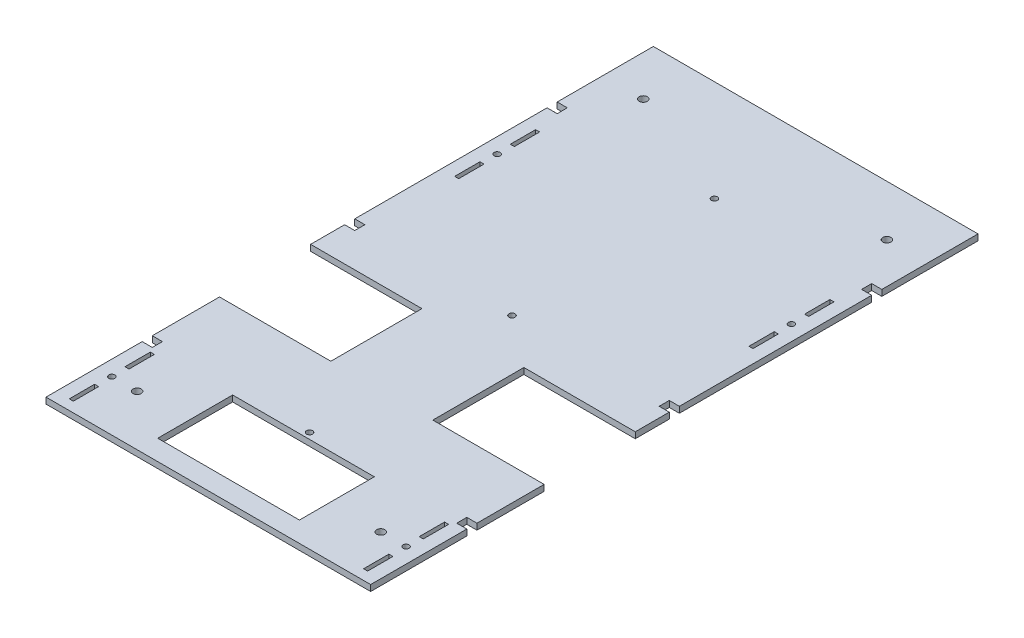
SolidWorks part; units mm, degrees
material "PMMA"
ref_plane "Front Plane" through (0, 0, 0) normal (0, 0, 1) x (1, 0, 0)
ref_plane "Top Plane" through (0, 0, 0) normal (0, 1, 0) x (1, 0, 0)
ref_plane "Right Plane" through (0, 0, 0) normal (1, 0, 0) x (0, 0, -1)
sketch "Schizzo1" plane through (0, 0, 0) normal (0, 1, 0) x (1, 0, 0)
  line L0 (-80.18, 150) -> (80.18, -150) construction
  line L1 (-80.18, 150) -> (80.18, 150)
  line L2 (-80.18, 150) -> (-80.18, -150)
  line L3 (-80.18, -150) -> (80.18, -150)
  line L4 (80.18, 150) -> (80.18, -150)
  point P4 (0, 0)
  dimension "D1" = 300
  dimension "D2" = 160.36
extrude "Estrusione-Estrusione1" add sketch "Schizzo1" along normal blind 3
sketch "Schizzo3" plane through (0, 0, 0) normal (0, 1, 0) x (1, 0, 0)
  line L0 (-80.18, 0) -> (80.18, 0) construction
  line L1 (-80.18, 150) -> (-80.18, -150) construction
  line L2 (0, 0) -> (0, -100) construction
  line L3 (0, 150) -> (0, -150) construction
  line L4 (80.18, 150) -> (-80.18, 150) construction
  line L5 (-80.18, -150) -> (80.18, -150) construction
  line L6 (0, 0) -> (0, 100) construction
  line L7 (-75.18, -97.5) -> (-80.18, -97.5)
  line L8 (-75.18, -2.5) -> (-80.18, -2.5)
  line L9 (-75.18, -2.5) -> (-75.18, 2.5)
  line L10 (-75.18, 2.5) -> (-80.18, 2.5)
  line L11 (-80.18, -2.5) -> (-80.18, 2.5)
  line L12 (-80.18, -102.5) -> (-80.18, -97.5)
  line L13 (-75.18, -102.5) -> (-80.18, -102.5)
  line L14 (-75.18, -102.5) -> (-75.18, -97.5)
  line L15 (-75.18, 2.5) -> (-75.18, -97.5) construction
  line L16 (-75.18, 97.5) -> (-80.18, 97.5)
  line L17 (-80.18, 97.5) -> (-80.18, 102.5)
  line L18 (-75.18, 102.5) -> (-80.18, 102.5)
  line L19 (-75.18, 97.5) -> (-75.18, 102.5)
  line L20 (-75.18, -2.5) -> (-75.18, 97.5) construction
  line L21 (75.18, -102.5) -> (75.18, -97.5)
  line L22 (75.18, -97.5) -> (80.18, -97.5)
  line L23 (80.18, -102.5) -> (80.18, -97.5)
  line L24 (75.18, -102.5) -> (80.18, -102.5)
  line L25 (75.18, -2.5) -> (75.18, 2.5)
  line L26 (75.18, 2.5) -> (80.18, 2.5)
  line L27 (80.18, -2.5) -> (80.18, 2.5)
  line L28 (75.18, -2.5) -> (80.18, -2.5)
  line L29 (75.18, 97.5) -> (75.18, 102.5)
  line L30 (75.18, 102.5) -> (80.18, 102.5)
  line L31 (80.18, 97.5) -> (80.18, 102.5)
  line L32 (75.18, 97.5) -> (80.18, 97.5)
  line L33 (-80.18, 150) -> (-80.18, -150) construction
  line L34 (-80.18, -19.3) -> (-25.18, -19.3)
  line L35 (-80.18, -19.3) -> (-80.18, -64.3)
  line L36 (-80.18, -64.3) -> (-25.18, -64.3)
  line L37 (-25.18, -19.3) -> (-25.18, -64.3)
  line L38 (80.18, -19.3) -> (80.18, -64.3)
  line L39 (80.18, -64.3) -> (25.18, -64.3)
  line L40 (25.18, -19.3) -> (25.18, -64.3)
  line L41 (80.18, -19.3) -> (25.18, -19.3)
  line L54 (80.18, -150) -> (80.18, 150) construction
  circle A0 centre (0, 0) radius 1.5
  circle A1 centre (0, -100) radius 1.5
  circle A2 centre (0, 100) radius 1.5
  circle A8 centre (-5.0427, -204.0432) radius 1.5
  point P24 (-80.18, 0)
  dimension "D1" = 3
  dimension "D2" = 100
  dimension "D4" = 100
  dimension "D5" = 5
  dimension "D6" = 5
  dimension "D7" = 100
  dimension "D9" = 100
  dimension "D11" = 55
  dimension "D12" = 45
  dimension "D13" = 16.8
  dimension "D3" = 2
  dimension "D8" = 2
  dimension "D10" = 2
extrude "Taglio-Estrusione1" cut sketch "Schizzo3" along direction (0, 1, 0) on the side of the normal through all
sketch "Schizzo4" plane through (0, 0, 0) normal (0, 1, 0) x (1, 0, 0)
  line L0 (-80.18, -102.5) -> (-80.18, -150) construction
  line L1 (-80.18, -150) -> (80.18, -150) construction
  line L2 (0, -150) -> (0, 150) construction
  line L3 (80.18, 150) -> (-80.18, 150) construction
  line L4 (75.18, 0) -> (-75.18, 0) construction
  line L5 (75.18, 2.5) -> (75.18, -2.5) construction
  line L6 (-75.18, -2.5) -> (-75.18, 2.5) construction
  circle A0 centre (-60.18, -125) radius 2
  circle A1 centre (60.18, -125) radius 2
  circle A2 centre (-60.18, 125) radius 2
  circle A3 centre (60.18, 125) radius 2
  dimension "D1" = 4
  dimension "D2" = 20
  dimension "D3" = 25
  dimension "D4" = 250
  dimension "D5" = 120.36
extrude "Taglio-Estrusione2" cut sketch "Schizzo4" along direction (0, 1, 0) on the side of the normal through all
sketch "Schizzo5" plane through (0, 0, 0) normal (0, 1, 0) x (1, 0, 0)
  line L0 (0, -150) -> (0, 150) construction
  line L1 (-80.18, -150) -> (80.18, -150) construction
  line L2 (80.18, 150) -> (-80.18, 150) construction
  line L3 (-80.18, -125) -> (80.18, -125) construction
  line L5 (80.18, -150) -> (80.18, -102.5) construction
  line L6 (-80.18, 65.35) -> (80.18, 65.35) construction
  line L7 (-80.18, 97.5) -> (-80.18, 2.5) construction
  line L8 (80.18, 2.5) -> (80.18, 97.5) construction
  line L10 (-80.18, 150) -> (-80.18, -19.3) construction
  line L11 (-80.18, -64.3) -> (-80.18, -150) construction
  line L12 (72.68, 72.85) -> (72.68, 57.85) construction
  line L13 (71.68, 85.35) -> (73.68, 85.35)
  line L14 (71.68, 85.35) -> (71.68, 72.85)
  line L15 (71.68, 72.85) -> (73.68, 72.85)
  line L16 (73.68, 85.35) -> (73.68, 72.85)
  line L17 (71.68, 57.85) -> (73.68, 57.85)
  line L18 (71.68, 57.85) -> (71.68, 45.35)
  line L19 (71.68, 45.35) -> (73.68, 45.35)
  line L20 (73.68, 57.85) -> (73.68, 45.35)
  line L21 (-71.68, 57.85) -> (-73.68, 57.85)
  line L22 (-71.68, 57.85) -> (-71.68, 45.35)
  line L23 (-71.68, 45.35) -> (-73.68, 45.35)
  line L24 (-73.68, 57.85) -> (-73.68, 45.35)
  line L25 (-71.68, 85.35) -> (-73.68, 85.35)
  line L26 (-71.68, 85.35) -> (-71.68, 72.85)
  line L27 (-71.68, 72.85) -> (-73.68, 72.85)
  line L28 (-73.68, 85.35) -> (-73.68, 72.85)
  line L29 (72.68, -117.5) -> (72.68, -132.5) construction
  line L30 (71.68, -105) -> (73.68, -105)
  line L31 (71.68, -105) -> (71.68, -117.5)
  line L32 (71.68, -117.5) -> (73.68, -117.5)
  line L33 (73.68, -105) -> (73.68, -117.5)
  line L34 (71.68, -132.5) -> (73.68, -132.5)
  line L35 (71.68, -132.5) -> (71.68, -145)
  line L36 (71.68, -145) -> (73.68, -145)
  line L37 (73.68, -132.5) -> (73.68, -145)
  line L38 (-71.68, -105) -> (-73.68, -105)
  line L39 (-71.68, -105) -> (-71.68, -117.5)
  line L40 (-71.68, -117.5) -> (-73.68, -117.5)
  line L41 (-73.68, -105) -> (-73.68, -117.5)
  line L42 (-71.68, -132.5) -> (-73.68, -132.5)
  line L43 (-71.68, -132.5) -> (-71.68, -145)
  line L44 (-71.68, -145) -> (-73.68, -145)
  line L45 (-73.68, -132.5) -> (-73.68, -145)
  circle A0 centre (72.68, 65.35) radius 1.5
  circle A1 centre (-72.68, 65.35) radius 1.5
  circle A2 centre (72.68, -125) radius 1.5
  circle A3 centre (-72.68, -125) radius 1.5
  dimension "D4" = 3
  dimension "D9" = 3
  dimension "D1" = 12.5
  dimension "D2" = 2
  dimension "D3" = 40
  dimension "D5" = 6.5
  dimension "D6" = 12.5
  dimension "D7" = 2
  dimension "D8" = 40
  dimension "D10" = 6.5
  dimension "D11" = 25
extrude "Taglio-Estrusione3" cut sketch "Schizzo5" along direction (0, 1, 0) on the side of the normal through all
sketch "Schizzo6" plane through (0, 0, 0) normal (0, 1, 0) x (1, 0, 0)
  line L1 (35, -140) -> (-35, -140)
  line L2 (35, -140) -> (35, -103)
  line L3 (35, -103) -> (-35, -103)
  line L4 (-35, -140) -> (-35, -103)
  line L6 (-80.18, -150) -> (80.18, -150) construction
  dimension "D1" = 37
  dimension "D2" = 70
  dimension "D3" = 35
  dimension "D4" = 10
extrude "Taglio-Estrusione4" cut sketch "Schizzo6" along direction (0, 1, 0) on the side of the normal through all
equation "\"Thickness2\"= 2"
equation "\"Thickness3\"=3"
equation "\"D1@Estrusione-Estrusione1\"=\"Thickness3\""
equation "\"D5@Schizzo3\"=\"Thickness5\""
equation "\"D6@Schizzo3\"=\"Thickness5\""
equation "\"Thickness5\"= 5"
equation "\"D2@Schizzo5\"= \"Thickness2\""
